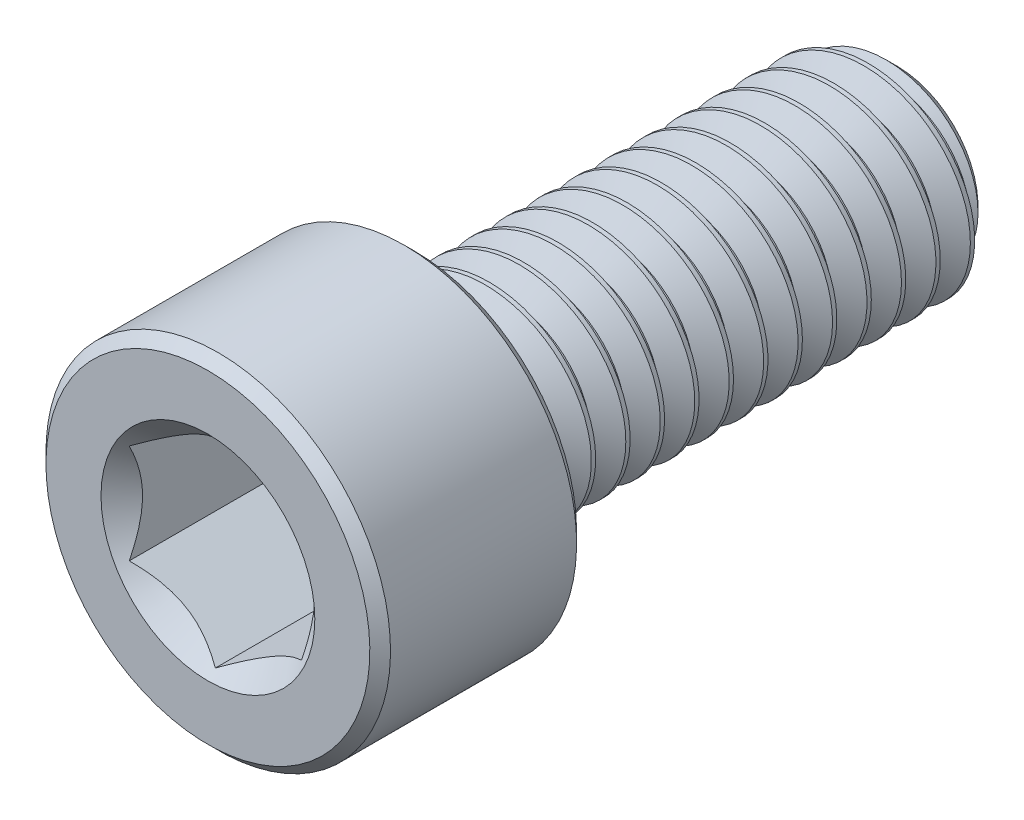
SolidWorks part; units mm, degrees
ref_plane "Front Plane" through (0, 0, 0) normal (0, 0, 1) x (1, 0, 0)
ref_plane "Top Plane" through (0, 0, 0) normal (0, 1, 0) x (1, 0, 0)
ref_plane "Right Plane" through (0, 0, 0) normal (1, 0, 0) x (0, 0, -1)
sketch "Sketch1" plane through (0, 0, 0) normal (1, 0, 0) x (0, 0, -1)
  line L0 (-10, 0) -> (10, 0) construction
  line L1 (10, 0) -> (10, 2.3505) construction
  line L2 (10, 2.3505) -> (9.3505, 3) construction
  line L3 (9.3505, 3) -> (9.25, 3) construction
  line L4 (9.25, 3) -> (-4, 3) construction
  line L5 (-4, 3) -> (-4, 5) construction
  line L6 (-4, 5) -> (-10, 5) construction
  line L7 (-10, 5) -> (-10, 0) construction
  line L8 (10, 2.3505) -> (10, 3) construction
  line L9 (9.9375, 3.1083) -> (10.4375, 2.2422) construction
  line L10 (10.4375, 2.2422) -> (10.9375, 3.1083) construction
  line L11 (10.9375, 3.1083) -> (9.9375, 3.1083) construction
  line L12 (10.4375, 3.1083) -> (10.4375, 3) construction
  line L13 (10.4375, 2.2422) -> (10.4375, 2.3505) construction
  line L14 (10.375, 2.3505) -> (10.5, 2.3505) construction
  line L15 (10, 3) -> (10.875, 3) construction
  line L16 (9.9687, 3.0541) -> (10.9062, 3.0541) construction
  line L17 (10, 0) -> (10, -3) construction
  line L18 (-4.3, 5) -> (-4, 4.7) construction
  line L19 (-9.7, 5) -> (-10, 4.7) construction
  line L20 (-4, 3) -> (-4, 0) construction
  line L21 (-4, 1.5) -> (0.6667, 1.5) construction
  line L22 (0.6667, 1.5) -> (5.3333, 1.5) construction
  line L23 (5.3333, 1.5) -> (10, 1.5) construction
  line L24 (0.6667, 1.5) -> (0.6667, 3) construction
  line L25 (0.6667, 3) -> (0.6667, 5) construction
  line L26 (5.3333, 1.5) -> (5.3333, 5) construction
  point P0 (-10, 2.5)
  point P3 (7.5, 3)
  point P4 (0, 0)
  point P18 (5.3333, 3)
  point P22 (10.4375, 2.3505)
  point P24 (9.25, 3)
  point P25 (10.4375, 3)
  point P28 (10.4375, 3.0541)
  point P29 (7.5, -3)
  point P30 (0.6667, 3)
  point P31 (-7, 5)
  point P37 (-5.05, 5)
  point P38 (-9.55, 5)
  point P45 (0.6667, 1.5)
  point P46 (5.3333, 1.5)
  dimension "D2" = 0.125
  dimension "D7" = 0.3
  dimension "D8" = 0.3
  dimension "D9" = 0.3
  dimension "D10" = 0.15
  dimension "D11" = 0.75
  dimension "Drive Size" = 5
  dimension "Head Diameter" = 10
  dimension "Head Height" = 6
  dimension "Thread Pitch" = 1
  dimension "Thread Dia" = 6
  dimension "Length" = 14
  dimension "D12" = 0.75
  dimension "D4" = 2.5
  dimension "D3" = 45
sketch "Sketch2" plane through (0, 0, 0) normal (1, 0, 0) x (0, 0, -1)
  line L0 (-10, 0) -> (-10, 4.7)
  line L1 (-9.7, 5) -> (-4.3, 5)
  line L2 (-4, 4.7) -> (-4, 3.3)
  line L4 (9.3505, 3) -> (10, 2.3505)
  line L5 (10, 2.3505) -> (10, 0)
  line L6 (-4, 5) -> (-10, 5) construction
  line L7 (10, 0) -> (-10, 0)
  line L8 (-9.7, 5) -> (-10, 4.7) construction
  line L10 (-9.7, 5) -> (-10, 4.7)
  line L14 (-4.3, 5) -> (-4, 4.7) construction
  line L16 (-4.3, 5) -> (-4, 4.7)
  line L17 (-4, 3) -> (-4, 5) construction
  line L19 (-3.7, 3) -> (9.3505, 3)
  line L20 (9.25, 3) -> (-4, 3) construction
  arc A1 (-4, 3.3) -> (-3.7, 3) centre (-3.7, 3.3) ccw
  dimension "D3" = 0.3
revolve "Revolve1" add sketch "Sketch2" angle 360 about L7
sketch "Sketch3" plane through (0, 0, 10) normal (0, 0, 1) x (1, 0, 0)
  line L1 (2.5, -1.4434) -> (2.5, 1.4434)
  line L2 (2.5, 1.4434) -> (0, 2.8868)
  line L3 (0, 2.8868) -> (-2.5, 1.4434)
  line L4 (-2.5, 1.4434) -> (-2.5, -1.4434)
  line L5 (-2.5, -1.4434) -> (0, -2.8868)
  line L6 (0, -2.8868) -> (2.5, -1.4434)
  circle A0 centre (0, 0) radius 2.5 construction
  circle A1 centre (0, 0) radius 5 construction
  circle A2 centre (0, 0) radius 5 construction
  circle A3 centre (0, 0) radius 2.8868 construction
  point P13 (0, 0)
  dimension "D1" = 5.7735
extrude "Cut-Extrude1" cut sketch "Sketch3" against normal offset from surface (5 mm away) 1 up to face at (0, 4.7, 4)
sketch "Sketch4" plane through (0, 0, 10) normal (0, 0, 1) x (1, 0, 0)
  circle A0 centre (0, 0) radius 3.1033
  dimension "D1" = 6.2065
extrude "Cut-Extrude2" cut sketch "Sketch4" against normal up to vertex (3 mm away) draft 45 up to point (0, 5, 7)
sketch "Sketch11" plane through (0, 0, 0) normal (1, 0, 0) x (0, 0, -1)
  line L0 (-10, 0) -> (10, 0) construction
  line L1 (-10, 0) -> (10, 0) construction
  line L2 (-1.375, 0) -> (-1.375, 3) construction
  line L3 (9.25, 3) -> (-4, 3) construction
  line L4 (7.375, 0) -> (7.375, 3) construction
  line L6 (10, 2.3505) -> (10, 3) construction
  point P2 (-1.375, 0)
  point P3 (7.375, 0)
  dimension "D1" = 2.625
  dimension "D2" = 2.625
sketch "Sketch6" plane through (0, 0, -10) normal (0, 0, -1) x (-1, 0, 0)
  circle A0 centre (0, 0) radius 3
curve "Helix/Spiral1" pitch 1 height 15 turns 15
sketch "Sketch10" plane through (0, 0, 0) normal (1, 0, 0) x (0, 0, -1)
  line L0 (-3.7, -5) -> (-3.7, 5)
  line L5 (-10, 0) -> (10, 0) construction
  line L6 (-3.7, 3) -> (-3.7, -3) construction
  point P3 (-3.7, 0)
split "Split1" trim tools "Sketch10" bodies to split 106 resulting bodies 114 115
sketch "Sketch7" plane through (0, 0, 0) normal (1, 0, 0) x (0, 0, -1)
  line L0 (9.9687, 3.0541) -> (10.9062, 3.0541)
  line L1 (10.9062, 3.0541) -> (10.5, 2.3505)
  line L2 (10.5, 2.3505) -> (10.375, 2.3505)
  line L3 (10.375, 2.3505) -> (9.9687, 3.0541)
sweep "Cut-Sweep1" cut profiles "Sketch7" path "Helix/Spiral1"
sketch "Sketch8" plane through (0, 0, 0) normal (1, 0, 0) x (0, 0, -1)
  line L0 (-4, 0) -> (-4, 3)
  line L1 (-3.7, -3) -> (-3.7, 3) construction
  line L2 (-4, 3) -> (-3.7, 3)
  line L4 (-3.7, 3) -> (-1.9679, 0)
  line L5 (-1.9679, 0) -> (-4, 0)
  line L6 (9.25, 3) -> (-4, 3) construction
  line L7 (-10, 0) -> (10, 0) construction
  dimension "D1" = 60
revolve "Revolve2" add sketch "Sketch8" angle 360 about L5
equation "\"D2@Sketch1\" = \"Thread Pitch@Sketch1\" / 8"
equation "\"D4@Helix/Spiral1\" = \"Thread Pitch@Sketch1\""
equation "\"D7@Sketch1\" = \"Head Height@Sketch1\" * .05"
equation "\"D8@Sketch1\"=\"D7@Sketch1\""
equation "\"D9@Sketch1\"=\"D7@Sketch1\""
equation "\"D10@Sketch1\"=\"D7@Sketch1\"/2"
equation "\"D11@Sketch1\"=\"D10@Sketch1\"*5"
equation "\"D4@Sketch1\"=\"Thread Pitch@Sketch1\"*2.5"
equation "\"D12@Sketch1\"=\"Thread Pitch@Sketch1\"*.75"
equation "\"D3@Helix/Spiral1\"=\"Length@Sketch1\"+\"Thread Pitch@Sketch1\""
equation "\"D3@Sketch2\"=\"Thread Dia@Sketch1\"*0.05"
equation "\"D1@Sketch11\"=\"Length@Sketch1\"*0.1875"
equation "\"D2@Sketch11\"=\"D1@Sketch11\""
equation "\"D1@Sketch4\"=\"D1@Sketch3\"*1.075"
